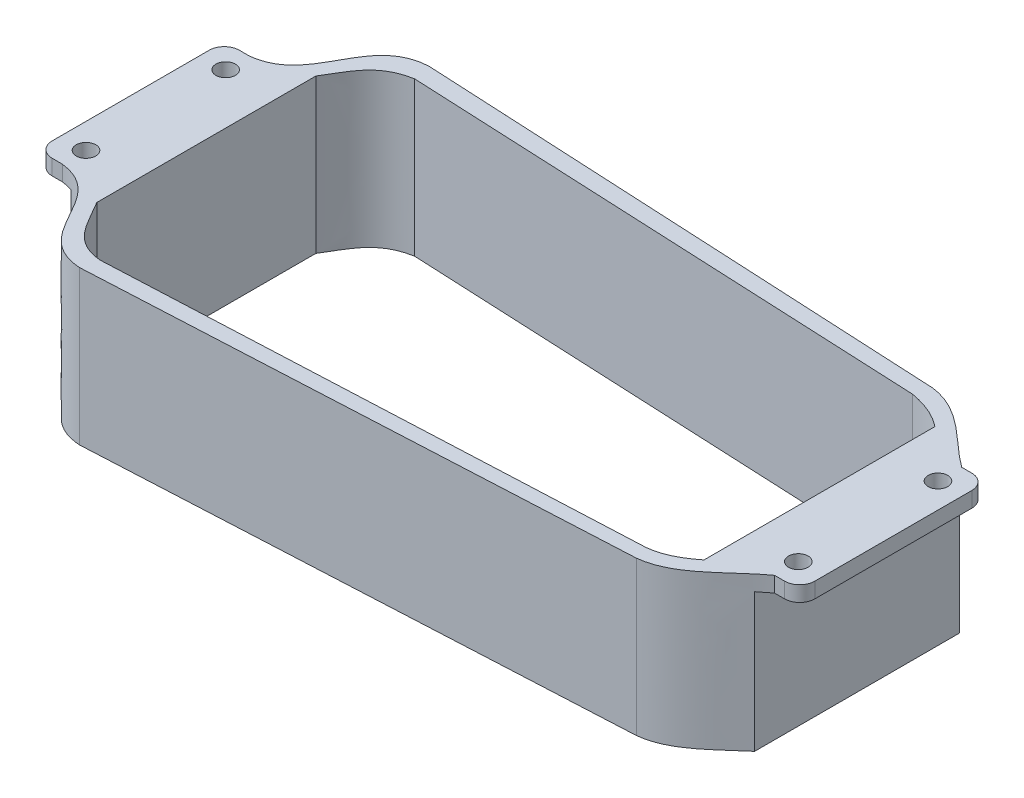
SolidWorks part; units mm, degrees
ref_plane "Front Plane" through (0, 0, 0) normal (0, 0, 1) x (1, 0, 0)
ref_plane "Top Plane" through (0, 0, 0) normal (0, 1, 0) x (1, 0, 0)
ref_plane "Right Plane" through (0, 0, 0) normal (1, 0, 0) x (0, 0, -1)
sketch "Sketch1" plane through (0, 0, 0) normal (0, 1, 0) x (1, 0, 0)
  line L0 (-77.09, -66.9326) -> (112.638, -57.3431)
  line L2 (-121.2974, 23.6569) -> (-121.2974, -32.5431)
  line L4 (151.7026, 23.6569) -> (151.7026, -32.5431)
  line L5 (-115.7974, -37.9431) -> (-115.8974, -37.9431)
  line L6 (-115.7974, -37.9431) -> (-112.2974, -37.9431)
  line L7 (-77.09, 58.0464) -> (112.638, 48.4569)
  line L8 (146.2026, -37.9431) -> (142.7026, -37.9431)
  line L9 (-115.7974, 29.0569) -> (-112.2974, 29.0569)
  line L10 (-115.7974, 29.0569) -> (-115.8974, 29.0569)
  line L11 (146.2026, 29.0569) -> (142.7026, 29.0569)
  line L12 (146.2026, 29.0569) -> (146.3026, 29.0569)
  line L13 (146.2026, -37.9431) -> (146.3026, -37.9431)
  line L14 (-75.6759, -60.9379) -> (111.224, -52.2979)
  line L19 (-75.6759, 51.5621) -> (111.224, 42.9221)
  line L26 (-94.2159, 34.7716) -> (-94.2159, -43.6579)
  line L27 (125.2889, 36.8927) -> (125.2889, -45.779)
  circle A0 centre (-112.2974, 20.5569) radius 3.5
  circle A1 centre (-112.2974, -29.4431) radius 3.5
  circle A2 centre (142.7026, -29.4431) radius 3.5
  circle A3 centre (142.7026, 20.5569) radius 3.5
  arc A4 (-115.8974, -37.9431) -> (-121.2974, -32.5431) centre (-115.8974, -32.5431) cw
  arc A5 (-115.8974, 29.0569) -> (-121.2974, 23.6569) centre (-115.8974, 23.6569) ccw
  arc A6 (146.3026, -37.9431) -> (151.7026, -32.5431) centre (146.3026, -32.5431) ccw
  arc A7 (146.3026, 29.0569) -> (151.7026, 23.6569) centre (146.3026, 23.6569) cw
  spline S0 degree 3 poles (-77.09, 58.0464) (-97.5029, 56.7625) (-92.6029, 31.2994) (-112.2974, 29.0569) knots 0 0 0 0 1 1 1 1
  spline S1 degree 3 poles (-77.09, -66.9326) (-97.5029, -65.6488) (-92.6029, -40.1856) (-112.2974, -37.9431) knots 0 0 0 0 1 1 1 1
  spline S2 degree 3 poles (112.638, 48.4569) (125.0826, 47.1415) (133.2878, 35.7758) (142.7026, 29.0569) knots 0 0 0 0 1 1 1 1
  spline S3 degree 3 poles (112.638, -57.3431) (125.0826, -56.0277) (133.2878, -44.662) (142.7026, -37.9431) knots 0 0 0 0 1 1 1 1
  spline S4 degree 3 poles (-75.6759, 51.5621) (-87.0119, 49.5172) (-89.587, 42.0382) (-94.2159, 34.7716) knots 0 0 0 0 0.624129 0.624129 0.624129 0.624129
  spline S5 degree 3 poles (-75.6759, -60.9379) (-87.0119, -60.0962) (-89.587, -50.9245) (-94.2159, -43.6579) knots 0 0 0 0 0.624129 0.624129 0.624129 0.624129
  spline S6 degree 3 poles (111.224, 42.9221) (116.6137, 41.9341) (121.1198, 40.1776) (125.2889, 36.8927) knots 0 0 0 0 0.481216 0.481216 0.481216 0.481216
  spline S7 degree 3 poles (111.224, -52.2979) (116.6137, -51.7282) (121.1198, -49.0639) (125.2889, -45.779) knots 0 0 0 0 0.481216 0.481216 0.481216 0.481216
  point P1 (17.774, 53.2516)
  point P8 (17.774, 47.2421)
  point P25 (17.774, -62.1379)
  point P43 (17.774, -56.6179)
  point P45 (-94.2159, -4.4431)
  point P46 (-121.2974, -4.4431)
  point P48 (125.2889, -4.4431)
  point P50 (151.7026, -4.4431)
  dimension "D1" = 27.0815
  dimension "D8" = 273
extrude "Boss-Extrude2" add sketch "Sketch1" against normal blind 55
sketch "Sketch7" plane through (-121.2974, 0, 0) normal (-1, 0, 0) x (0, 0, 1)
  line L0 (-23.6569, 0) -> (32.5431, 0) construction
  line L1 (-30.1667, -5.5) -> (38.8329, -5.5)
  line L2 (-30.1667, -5.5) -> (-30.1667, -55.9156)
  line L3 (-30.1667, -55.9156) -> (38.8329, -55.9156)
  line L4 (38.8329, -5.5) -> (38.8329, -55.9156)
  dimension "D1" = 68.9997
  dimension "D2" = 5.5
extrude "Cut-Extrude5" cut sketch "Sketch7" against normal blind 13
sketch "Sketch19" plane through (151.7026, 0, 0) normal (1, 0, 0) x (0, 0, -1)
  line L0 (-32.5431, 0) -> (23.6569, 0) construction
  line L1 (-42.5272, -5.5) -> (32.3322, -5.5)
  line L2 (-42.5272, -5.5) -> (-42.5272, -66.2251)
  line L3 (-42.5272, -66.2251) -> (32.3322, -66.2251)
  line L4 (32.3322, -5.5) -> (32.3322, -66.2251)
  dimension "D1" = 5.5
extrude "Cut-Extrude7" cut sketch "Sketch19" against normal blind 13
